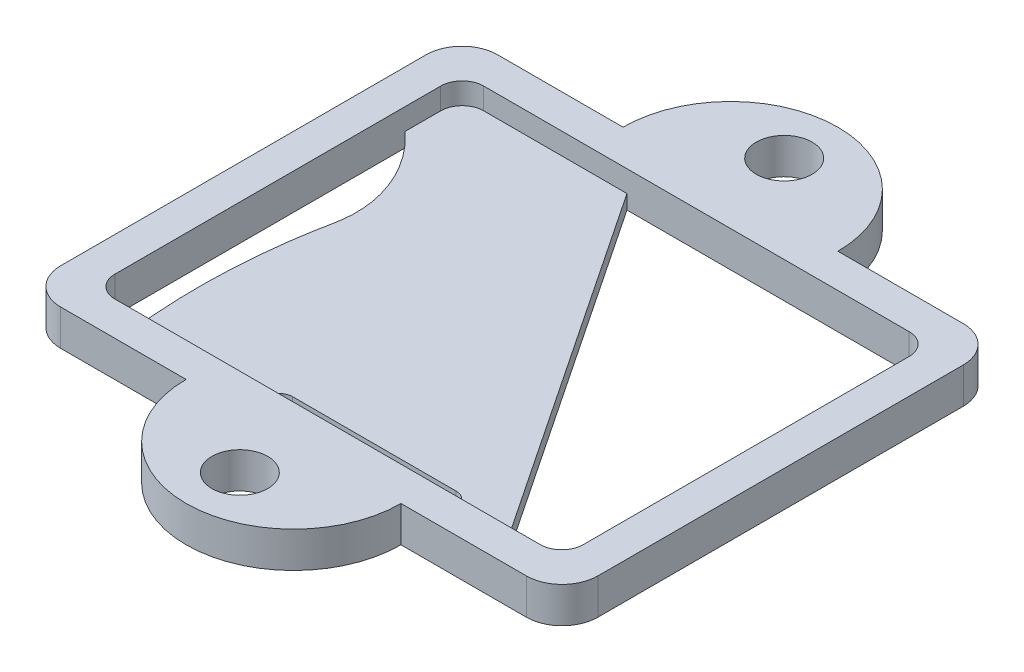
SolidWorks part; units mm, degrees
ref_plane "Front Plane" through (0, 0, 0) normal (0, 0, 1) x (1, 0, 0)
ref_plane "Top Plane" through (0, 0, 0) normal (0, 1, 0) x (1, 0, 0)
ref_plane "Right Plane" through (0, 0, 0) normal (1, 0, 0) x (0, 0, -1)
sketch "Sketch1" plane through (0, 0, 0) normal (0, 1, 0) x (1, 0, 0)
  line L0 (-37.5, 76) -> (-37.5, 61)
  line L1 (0, 0) -> (-75, 0)
  line L2 (0, 0) -> (0, 61)
  line L3 (0, 61) -> (-75, 61)
  line L4 (-75, 0) -> (-75, 61)
  line L5 (0, 30.5) -> (-75, 30.5) construction
  line L6 (-22.5, 61) -> (-52.5, 61)
  arc A0 (-22.5, 61) -> (-52.5, 61) centre (-37.5, 61) ccw
  circle A1 centre (-37.5, 68.5) radius 3.9
  circle A2 centre (-37.5, -7.5) radius 3.9
  arc A3 (-22.5, 0) -> (-52.5, 0) centre (-37.5, 0) cw
  dimension "D4" = 7.8
  dimension "D1" = 75
  dimension "D2" = 61
extrude "Boss-Extrude1" add sketch "Sketch1" along normal blind 5 contours L5 L2 L3 L4 | L2 L5 L4 L1 | A1 L0 L3 A0 | A1 L0 A0 L3 | A3 L1 A2
sketch "Sketch2" plane through (0, 5, 0) normal (0, 1, 0) x (1, 0, 0)
  line L0 (-75, 61) -> (0, 0)
  line L2 (-70.2, 4.75) -> (-4.8, 4.75)
  line L3 (-70.2, 4.75) -> (-70.2, 56.25)
  line L4 (-70.2, 56.25) -> (-4.8, 56.25)
  line L5 (-4.8, 4.75) -> (-4.8, 56.25)
  line L6 (-70.2, 4.75) -> (-4.8, 56.25) construction
  line L7 (-70.2, 56.25) -> (-4.8, 4.75) construction
  point P4 (-37.5, 30.5)
  dimension "D1" = 51.5
  dimension "D2" = 65.4
extrude "Cut-Extrude1" cut sketch "Sketch2" against normal blind 3 contours L4 L3 L2 L0 | L2 L5 L4 L0
sketch "Sketch3" plane through (0, 2, 0) normal (0, 1, 0) x (1, 0, 0)
  line L0 (-70.2, 56.25) -> (-62.2, 56.25)
  line L1 (-70.2, 56.25) -> (-4.8, 56.25) construction
  line L2 (-70.2, 4.75) -> (-65.2, 4.75)
  line L3 (-70.2, 4.75) -> (-4.8, 4.75) construction
  line L4 (-70.2, 48.25) -> (-70.2, 56.25)
  line L5 (-47.2, 56.25) -> (-4.8, 56.25)
  line L6 (-4.8, 56.25) -> (-4.8, 4.75)
  line L7 (-70.2, 4.75) -> (-70.2, 56.25) construction
  line L8 (-4.8, 56.25) -> (-12.8, 56.25)
  line L9 (-4.8, 4.75) -> (-12.8, 4.75)
  line L10 (-62.2, 56.25) -> (-47.2, 56.25)
  line L11 (-47.2, 56.25) -> (-12.8, 4.75)
  line L12 (-65.2, 4.75) -> (-70.2, 4.75)
  line L13 (-12.8, 4.75) -> (-65.2, 4.75)
  line L14 (-70.2, 48.25) -> (-70.2, 4.75)
  line L15 (-47.7958, 4.75) -> (-21.3412, 4.75)
  line L17 (-45.9958, 8.35) -> (-23.1412, 8.35)
  line L18 (-45.9958, 4.75) -> (-23.1412, 4.75)
  line L19 (-47.7958, 6.55) -> (-47.7958, 4.75)
  line L20 (-47.7958, 4.75) -> (-45.9958, 4.75)
  line L21 (-21.3412, 6.55) -> (-21.3412, 4.75)
  line L22 (-21.3412, 4.75) -> (-23.1412, 4.75)
  arc A0 (-45.9958, 8.35) -> (-47.7958, 6.55) centre (-45.9958, 6.55) ccw
  arc A1 (-21.3412, 6.55) -> (-23.1412, 8.35) centre (-23.1412, 6.55) ccw
  spline S1 degree 2 poles (-70.2, 48.25) (-69.336, 47.3934) (-68.4842, 46.5269) knots 0 0 0 0.044513 0.044513 0.044513
  spline S3 degree 3 poles (-65.2, 4.75) (-66.2859, 14.1334) (-65.9061, 23.3434) (-64.0606, 32.38) knots 0 0 0 0 0.783885 0.783885 0.783885 0.783885
  spline S4 degree 3 poles (-70.2, 48.25) (-65.781, 44.3104) (-62.8458, 38.2212) (-64.083, 32.2702) knots 0 0 0 0 1 1 1 1
  point P28 (-34.5685, 6.55)
  line M3 (-4.8, 56.25) -> (-70.2, 56.25)
  line M4 (-70.2, 56.25) -> (-70.2, 4.75)
  line M5 (-70.2, 4.75) -> (-4.8, 4.75)
  line M6 (-4.8, 4.75) -> (-4.8, 56.25)
  dimension "D5" = 1.8
  dimension "D1" = 8
  dimension "D2" = 5
  dimension "D3" = 8
  dimension "D4" = 15
extrude "Cut-Extrude2" cut sketch "Sketch3" against normal through all contours S4 S1 S3 M4 M5 | L5 L11 M5 M6 M3 | L21 A1 L17 A0 L19 L13 L15
fillet "Fillet1" radius 5 4 edges at (-75, 2.5, -61) (0, 2.5, -61) (0, 2.5, 0) (-75, 2.5, 0)
fillet "Fillet2" radius 3 4 edges at (-70.2, 3.5, -56.25) (-70.2, 2.5, -4.75) (-4.8, 2.5, -4.75) (-4.8, 2.5, -56.25)
